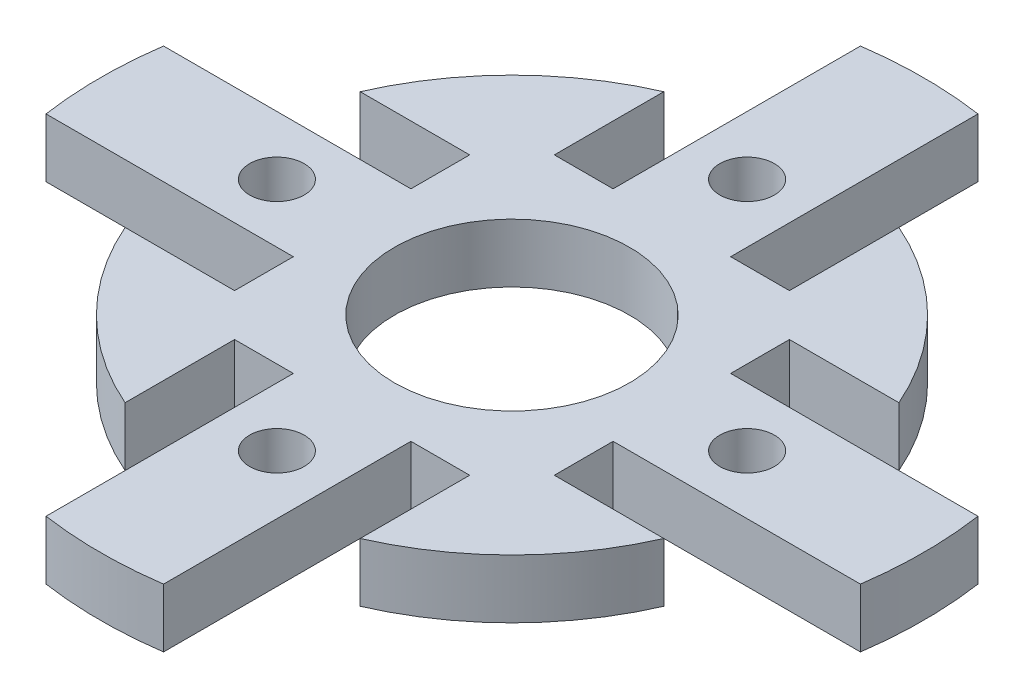
SolidWorks part; units mm, degrees
ref_plane "Front Plane" through (0, 0, 0) normal (0, 0, 1) x (1, 0, 0)
ref_plane "Top Plane" through (0, 0, 0) normal (0, 1, 0) x (1, 0, 0)
ref_plane "Right Plane" through (0, 0, 0) normal (1, 0, 0) x (0, 0, -1)
sketch "Sketch1" plane through (0, 0, 0) normal (0, 1, 0) x (1, 0, 0)
  line L0 (-3.175, 21.997) -> (-3.175, 15.5543)
  line L1 (3.175, 21.997) -> (3.175, 15.5543)
  line L2 (-3.175, 18.241) -> (3.175, 18.241) construction
  line L3 (21.997, 3.175) -> (15.5543, 3.175)
  line L4 (21.997, -3.175) -> (15.5543, -3.175)
  line L5 (18.241, 3.175) -> (18.241, -3.175) construction
  line L6 (3.175, -21.997) -> (3.175, -15.5543)
  line L7 (-3.175, -21.997) -> (-3.175, -15.5543)
  line L8 (3.175, -18.241) -> (-3.175, -18.241) construction
  line L9 (-21.997, -3.175) -> (-15.5543, -3.175)
  line L10 (-21.997, 3.175) -> (-15.5543, 3.175)
  line L11 (-18.241, -3.175) -> (-18.241, 3.175) construction
  line L12 (-3.175, 15.5543) -> (-3.175, 8.4206)
  line L13 (-3.175, 8.4206) -> (-5.9765, 8.4206)
  arc A0 (3.175, 5.4993) -> (-3.175, 5.4993) centre (0, 0) ccw
  arc A1 (3.175, 21.997) -> (-3.175, 21.997) centre (0, 0) ccw
  arc A2 (5.4993, -3.175) -> (5.4993, 3.175) centre (0, 0) ccw
  arc A3 (21.997, -3.175) -> (21.997, 3.175) centre (0, 0) ccw
  arc A4 (-3.175, -5.4993) -> (3.175, -5.4993) centre (0, 0) ccw
  arc A5 (-3.175, -21.997) -> (3.175, -21.997) centre (0, 0) ccw
  arc A6 (-5.4993, 3.175) -> (-5.4993, -3.175) centre (0, 0) ccw
  arc A7 (-21.997, 3.175) -> (-21.997, -3.175) centre (0, 0) ccw
  circle A8 centre (0, 0) radius 6.35
  arc A9 (-15.5543, -3.175) -> (-3.175, -15.5543) centre (0, 0) ccw
  arc A10 (-3.175, 15.5543) -> (-15.5543, 3.175) centre (0, 0) ccw
  arc A11 (15.5543, 3.175) -> (3.175, 15.5543) centre (0, 0) ccw
  arc A12 (3.175, -15.5543) -> (15.5543, -3.175) centre (0, 0) ccw
  point P10 (0, 18.241)
  point P30 (0, 0)
  dimension "D1" = 12.7
  dimension "D2" = 44.45
  dimension "D5" = 9.525
  dimension "D3" = 6.35
  dimension "D4" = 4
extrude "Boss-Extrude1" add sketch "Sketch1" along normal blind 3.175 contours L6 A12 L4 A3 L3 A11 L1 A1 L0 A10 L10 A7 L9 A9 L7 A5 A8 A4 A6 A0 A2
sketch "Sketch2" plane through (-1.4932, 3.175, -17.338) normal (0, 1, 0) x (1, 0, 0)
  line L0 (1.4932, -0.6692) -> (1.4932, -8.6067) construction
  line L1 (1.4932, -23.688) -> (1.4932, -36.388) construction
  circle A0 centre (1.4932, -0.6692) radius 0.762
  circle A1 centre (1.4932, -8.6067) radius 0.762
  circle A2 centre (1.4932, -4.638) radius 1.9812
  circle A3 centre (1.4932, -17.338) radius 12.7 construction
  circle A5 centre (1.4932, -17.338) radius 19.05 construction
  arc A7 (4.6682, -11.8387) -> (-1.6818, -11.8387) centre (1.4932, -17.338) ccw construction
  circle A9 centre (1.4932, -17.338) radius 6.35 construction
  point P0 (1.4932, -0.6692)
  point P1 (1.4932, -8.6067)
  point P2 (1.4932, -4.638)
  point P18 (1.4932, -30.038)
  dimension "D2" = 1.524
  dimension "D3" = 3.9624
  dimension "D4" = 12.7
  dimension "D5" = 38.1
  dimension "D1" = 7.9375
hole_wizard "1/16 (0.0625) Press Dowel Hole1" positions "Sketch4" profile "Sketch6" hole size "1/16" standard "ANSI Inch"
sketch "Sketch4" plane through (-5.4161, 3.175, 1.0254) normal (0, 1, 0) x (1, 0, 0)
  point P0 (5.4161, 17.6941)
  point P3 (5.4161, 9.7566)
sketch "Sketch6" plane through (0, 3.175, -16.6688) normal (1, 0, 0) x (0, 0, 1)
  line L0 (0, 0) -> (0, 3.176)
  line L1 (0, 3.176) -> (0.762, 3.176)
  line L2 (0.762, 3.176) -> (0.762, 0)
  line L5 (0.762, 0) -> (0, 0)
  line L11 (0, -6.35) -> (0, 107.95) construction
  dimension "Thru Hole Dia." = 1.524
  dimension "Thru Hole Depth" = 3.176
hole_wizard "#4 Clearance Hole1" positions "Sketch8" profile "Sketch10" hole size "#4" standard "ANSI Inch" end condition through all
sketch "Sketch8" plane through (-5.1529, 3.175, -13.7417) normal (0, 1, 0) x (1, 0, 0)
  point P0 (5.1529, -1.0417)
sketch "Sketch10" plane through (0, 3.175, -12.7) normal (1, 0, 0) x (0, 0, 1)
  line L0 (0, 0) -> (0, 3.175)
  line L1 (0, 3.175) -> (1.4732, 3.175)
  line L2 (1.4732, 3.175) -> (1.4732, 0)
  line L5 (1.4732, 0) -> (0, 0)
  line L11 (0, -6.35) -> (0, 107.95) construction
  dimension "Thru Hole Dia." = 2.9464
  dimension "Thru Hole Depth" = 3.175
sketch "Sketch11" plane through (0, 3.175, 0) normal (0, 1, 0) x (1, 0, 0)
  line L1 (-3.175, 8.636) -> (-6.35, 8.636)
  line L2 (-3.175, 8.636) -> (-3.175, 15.5543)
  line L3 (-3.175, 15.5543) -> (-6.35, 15.5543)
  line L4 (-6.35, 8.636) -> (-6.35, 15.5543)
  line L5 (-3.175, 8.636) -> (-6.35, 15.5543) construction
  line L6 (-3.175, 15.5543) -> (-6.35, 8.636) construction
  point P0 (-4.7625, 12.0951)
  dimension "D1" = 3.175
  dimension "D2" = 8.636
extrude "Cut-Extrude1" cut sketch "Sketch11" against normal up to next
mirror "Mirror1" about plane through (0, 0, 0) normal (1, 0, 0) of "Cut-Extrude1"
pattern_circular "CirPattern2" count 4 over 360 about axis through (0, 0, 0) along (0, 1, 0) of "#4 Clearance Hole1", "1/16 (0.0625) Press Dowel Hole1", "Mirror1"
